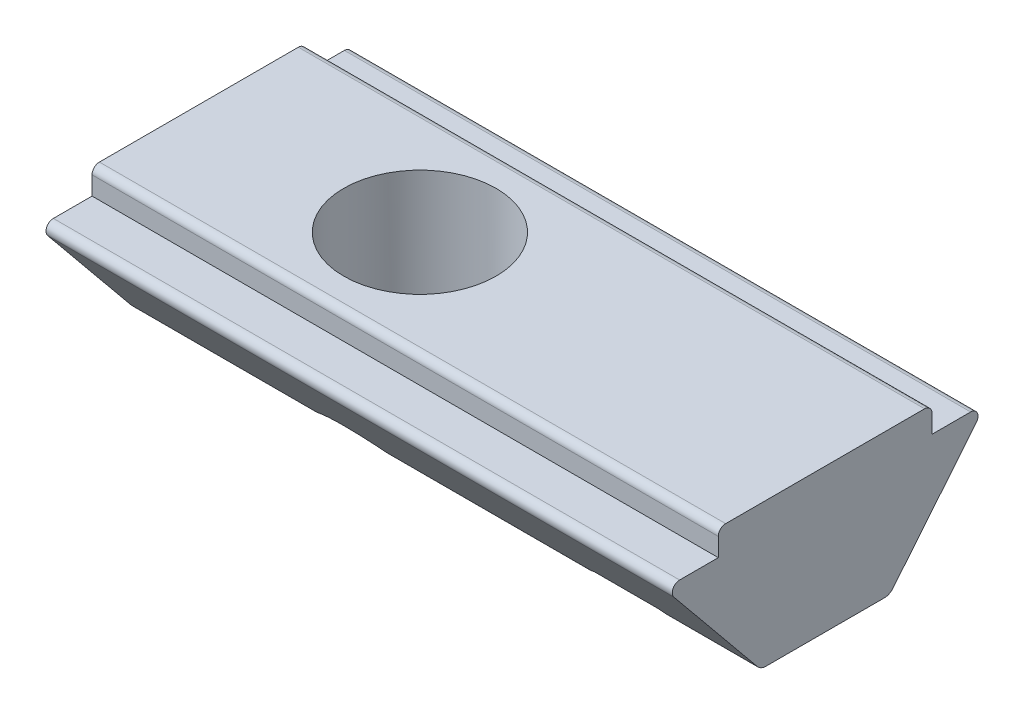
SolidWorks part; units mm, degrees
ref_plane "Front Plane" through (0, 0, 0) normal (0, 0, 1) x (1, 0, 0)
ref_plane "Top Plane" through (0, 0, 0) normal (0, 1, 0) x (1, 0, 0)
ref_plane "Right Plane" through (0, 0, 0) normal (1, 0, 0) x (0, 0, -1)
ref_plane "Plane1" through (-6, 0, 0) normal (1, 0, 0) x (0, 0, -1)
ref_plane "Plane2" through (7.5, 0, 0) normal (1, 0, 0) x (0, 0, -1)
ref_plane "Plane3" through (-3.1, 0, 0) normal (1, 0, 0) x (0, 0, -1)
sketch "Sketch1" plane through (-6, 0, 0) normal (1, 0, 0) x (0, 0, -1)
  line L0 (2.9, 0) -> (-2.9, 0)
  line L1 (-2.9, 0) -> (-2.9, -0.7)
  line L2 (-2.9, -0.7) -> (-3.95, -0.7)
  line L3 (4.15, 0) -> (4.15, -3.9) construction
  line L4 (-4.1047, -1.0268) -> (-1.75, -3.9)
  line L5 (-1.75, -3.9) -> (1.75, -3.9)
  line L6 (1.75, -3.9) -> (4.1047, -1.0268)
  line L7 (-4.15, 0) -> (-4.15, -3.9) construction
  line L8 (3.95, -0.7) -> (2.9, -0.7)
  line L9 (2.9, -0.7) -> (2.9, 0)
  line L10 (0, 0) -> (0, -3.9) construction
  arc A2 (-4.1047, -1.0268) -> (-3.95, -0.7) centre (-3.95, -0.9) cw
  arc A3 (4.1047, -1.0268) -> (3.95, -0.7) centre (3.95, -0.9) ccw
  point P18 (-1.75, -3.9)
  point P21 (1.75, -3.9)
  dimension "FIX_7" = 3.5
  dimension "FIX_5" = 0.2
  dimension "FIX_2" = 5.8
  dimension "FIX_3" = 3.9
  dimension "FIX_4" = 3.2
  dimension "FIX_6" = 8.3
extrude "Boss-Extrude1" add sketch "Sketch1" along normal blind 17
fillet "Fillet1" radius 0.3 2 edges at (2.5, -3.9, 1.75) (2.5, -3.9, -1.75)
fillet "Fillet2" radius 0.2 2 edges at (2.5, 0, 2.9) (2.5, 0, -2.9)
sketch "Sketch2" plane through (7.5, 0, 0) normal (1, 0, 0) x (0, 0, -1)
  line L0 (0, 1.6655) -> (0, -9.505) construction
  line L2 (0, -3.7) -> (2.1, -3.7)
  line L3 (0, -3.7) -> (0, -3.9)
  line L4 (0, -3.9) -> (2.1, -3.9)
  line L5 (2.1, -3.7) -> (2.1, -3.9)
  dimension "FIX_11" = 0.2
  dimension "FIX_12" = 2.1
  dimension "FIX_13" = 3.9
revolve "Cut-Revolve1" cut sketch "Sketch2" angle 360 about L0
sketch "Sketch3" plane through (7.5, 0, 0) normal (1, 0, 0) x (0, 0, -1)
  line L0 (0, 0) -> (0, -4.7) construction
  line L1 (1.7321, -3.7) -> (0, -3.7) construction
  line L2 (1.7321, -4.7) -> (0, -4.7) construction
  line L3 (1.7321, -3.7) -> (0, -3.7)
  line L4 (0, -3.7) -> (0, -4.7)
  arc A0 (0, -4.7) -> (1.7321, -3.7) centre (0, -2.7) ccw
  dimension "FIX_15" = 4
  dimension "FIX_16" = 4.7
  dimension "FIX_17" = 3.7
revolve "Revolve1" add sketch "Sketch3" angle 360 about L0
hole_wizard "Tapped Hole1" positions "Sketch5" profile "Sketch4" tap size "M5x0.8" standard "JIS" end condition through all
sketch "Sketch5" plane through (0, 0, 0) normal (0, 1, 0) x (1, 0, 0)
  point P0 (0, 0)
sketch "Sketch4" plane through (0, 0, 0) normal (1, 0, 0) x (0, 0, 1)
  line L0 (0, 0) -> (0, 4.7)
  line L1 (0, 4.7) -> (2.067, 4.7)
  line L2 (2.067, 4.7) -> (2.067, 0)
  line L5 (2.067, 0) -> (0, 0)
  line L11 (0, -6.35) -> (0, 107.95) construction
  dimension "Thru Tap Drill Dia." = 4.134
  dimension "Thru Tap Drill Depth" = 4.7
cosmetic thread "Thread1" parameters "M"=5
sketch "Sketch6" [suppressed] plane through (-3.1, 0, 0) normal (1, 0, 0) x (0, 0, -1)
  line L0 (3.4, -0.6) -> (3.4, -0.7) construction
  line L1 (3.4, -0.6) -> (3.4, -0.7)
  line L2 (3.4, -0.7) -> (3.5, -0.7)
  arc A0 (3.5, -0.7) -> (3.4, -0.6) centre (3.4, -0.7) ccw
  dimension "FIX_19" = 0.1
  dimension "FIX_20" = 0.7
  dimension "FIX_21" = 3.4
revolve "Revolve2" [suppressed] add sketch "Sketch6" angle 360 about L0
pattern_linear "LPattern1" [suppressed]
